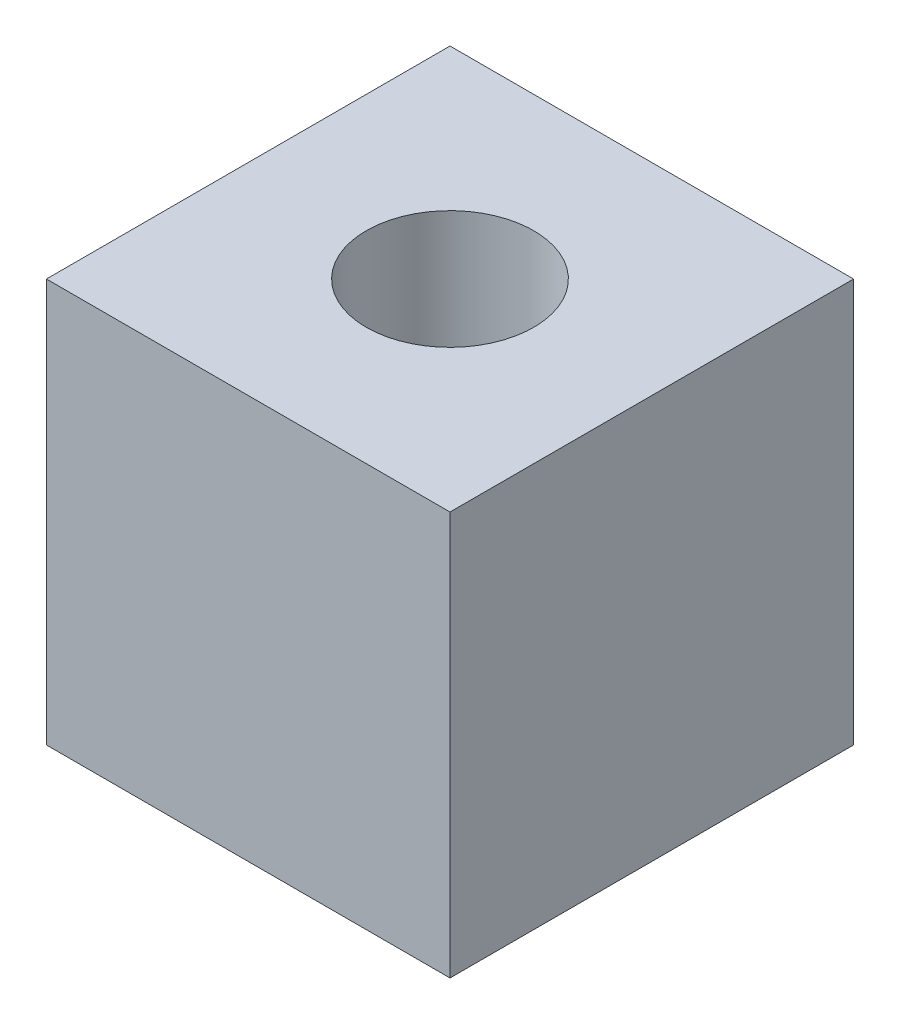
SolidWorks part; units mm, degrees
ref_plane "Front Plane" through (0, 0, 0) normal (0, 0, 1) x (1, 0, 0)
ref_plane "Top Plane" through (0, 0, 0) normal (0, 1, 0) x (1, 0, 0)
ref_plane "Right Plane" through (0, 0, 0) normal (1, 0, 0) x (0, 0, -1)
sketch "Sketch1" plane through (0, 0, 0) normal (0, 1, 0) x (1, 0, 0)
  line L1 (0, 0) -> (-20, 0)
  line L2 (0, 0) -> (0, 20)
  line L3 (0, 20) -> (-20, 20)
  line L4 (-20, 0) -> (-20, 20)
  dimension "D1" = 20
  dimension "D2" = 20
extrude "Boss-Extrude1" add sketch "Sketch1" along normal blind 20
sketch "Sketch2" plane through (0, 20, 0) normal (0, 1, 0) x (1, 0, 0)
  line L0 (-20, 10) -> (0, 10) construction
  line L1 (-20, 20) -> (-20, 0) construction
  line L2 (0, 0) -> (0, 20) construction
  circle A0 centre (-10, 10) radius 4.15
  dimension "D1" = 8.3
extrude "Cut-Extrude1" cut sketch "Sketch2" against normal through all
